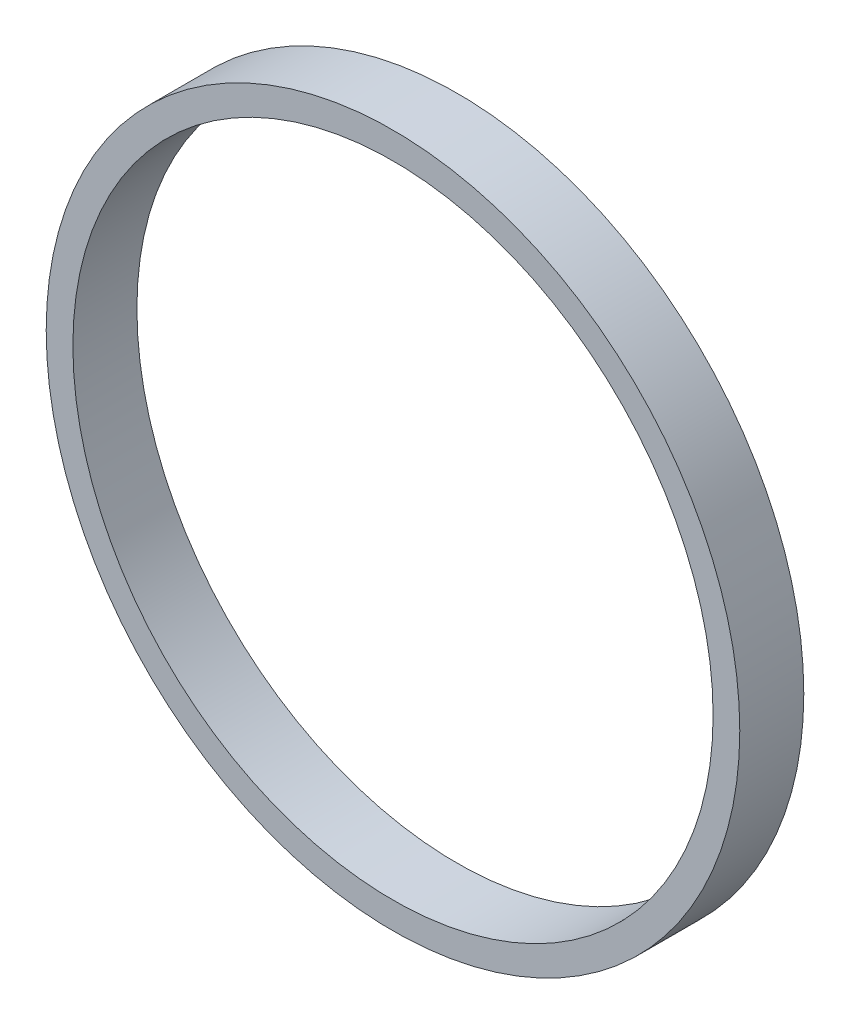
SolidWorks part; units mm, degrees
ref_plane "Front Plane" through (0, 0, 0) normal (0, 0, 1) x (1, 0, 0)
ref_plane "Top Plane" through (0, 0, 0) normal (0, 1, 0) x (1, 0, 0)
ref_plane "Right Plane" through (0, 0, 0) normal (1, 0, 0) x (0, 0, -1)
sketch "Sketch1" plane through (0, 0, 0) normal (0, 0, 1) x (1, 0, 0)
  circle A0 centre (0, 0) radius 30
  circle A1 centre (0, 0) radius 32.5
  dimension "D1" = 65
  dimension "D2" = 60
extrude "Boss-Extrude1" add sketch "Sketch1" along normal mid plane 6
